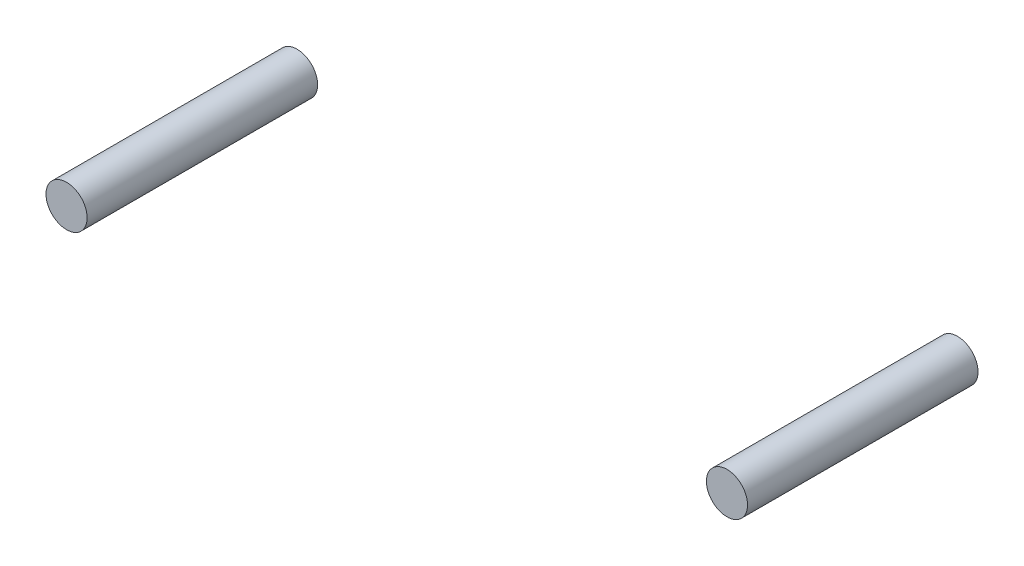
SolidWorks part; units mm, degrees
ref_plane "Front Plane" through (0, 0, 0) normal (0, 0, 1) x (1, 0, 0)
ref_plane "Top Plane" through (0, 0, 0) normal (0, 1, 0) x (1, 0, 0)
ref_plane "Right Plane" through (0, 0, 0) normal (1, 0, 0) x (0, 0, -1)
surface "Surface-Offset1" parameters "D1"=0
ref_plane "Plane1" through (0, 0, 48.2981) normal (0, 0, 1) x (1, 0, 0)
ref_plane "Plane2" through (0, 0, -22.86) normal (0, 0, -1) x (-1, 0, 0)
sketch "Sketch2" plane through (0, 0, -22.86) normal (0, 0, -1) x (-1, 0, 0)
  circle A0 centre (203.8888, -25.1744) radius 6.35 construction
  circle A1 centre (0, 0) radius 6.35 construction
  circle A2 centre (203.8888, -25.1744) radius 6.35
  circle A3 centre (0, 0) radius 6.35
extrude "Boss-Extrude1" add sketch "Sketch2" against normal up to surface (71.1581 mm away) up to plane "Plane1"
